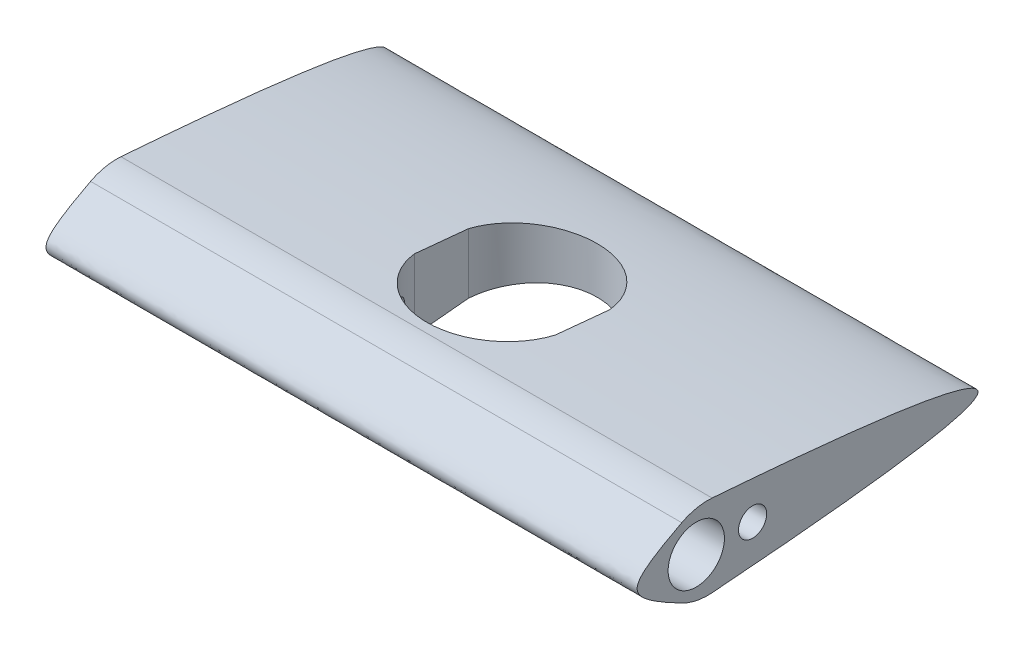
SolidWorks part; units mm, degrees
ref_plane "Front Plane" through (0, 0, 0) normal (0, 0, 1) x (1, 0, 0)
ref_plane "Top Plane" through (0, 0, 0) normal (0, 1, 0) x (1, 0, 0)
ref_plane "Right Plane" through (0, 0, 0) normal (1, 0, 0) x (0, 0, -1)
sketch "Sketch1" plane through (0, 0, 0) normal (1, 0, 0) x (0, 0, -1)
  line L0 (0, -7.6228) -> (0, 2.3772) construction
  line L1 (0, -7.5) -> (0, 7.5) construction
  line L2 (0, 0) -> (-15, 0) construction
  line L3 (0, 0) -> (50, 0) construction
  line L4 (50, 0) -> (75, 0) construction
  line L5 (75, 0) -> (100, 0) construction
  circle A0 centre (0, 0) radius 5
  circle A1 centre (10, 0) radius 2.5
  conic Q0 (0, 7.5) -> (0, -7.5) control (-15, 0) rho 0.7
  conic Q1 (0, 7.5) -> (0, -7.5) control (100, 0) rho 0.500367
  point P8 (0, 0)
  dimension "D1" = 10
  dimension "D7" = 5
  dimension "D2" = 15
  dimension "D3" = 15
  dimension "D4" = 50
  dimension "D5" = 25
  dimension "D6" = 25
  dimension "D8" = 10
extrude "Boss-Extrude1" add sketch "Sketch1" along normal blind 105
fillet "Fillet1" radius 10 2 edges at (52.5, 7.5, 0) (52.5, -7.5, 0)
sketch "Sketch2" plane through (0, 0, 0) normal (0, 1, 0) x (1, 0, 0)
  line L0 (0, 2.8086) -> (0, -2.5828) construction
  line L1 (0, -2.5828) -> (0, -10.5) construction
  line L2 (0, -10.5) -> (105, -10.5) construction
  line L3 (105, -10.5) -> (105, -2.5828) construction
  line L4 (105, -2.5828) -> (105, 2.8086) construction
  line L5 (105, 2.8086) -> (105, 50.0367) construction
  line L6 (105, 50.0367) -> (0, 50.0367) construction
  line L7 (0, 50.0367) -> (0, 2.8086) construction
  line L8 (0, 2.8086) -> (0, -2.5828)
  line L9 (0, -2.5828) -> (0, -10.5)
  line L10 (0, -10.5) -> (105, -10.5)
  line L11 (105, -10.5) -> (105, -2.5828)
  line L12 (105, -2.5828) -> (105, 2.8086)
  line L13 (105, 2.8086) -> (105, 50.0367)
  line L14 (105, 50.0367) -> (0, 50.0367)
  line L15 (0, 50.0367) -> (0, 2.8086)
  line L16 (40, 19.7683) -> (65, 19.7683) construction
  line L17 (40, -10.5) -> (65, -10.5)
  line L18 (40, -10.5) -> (40, 50.0367)
  line L19 (40, 50.0367) -> (65, 50.0367)
  line L20 (65, -10.5) -> (65, 50.0367)
  line L21 (40, -10.5) -> (65, 50.0367) construction
  line L22 (40, 50.0367) -> (65, -10.5) construction
  line L23 (52.5, 19.7683) -> (52.5, 50.0367) construction
  line L24 (52.5, -10.5) -> (52.5, 19.7683) construction
  line L25 (65, 34.9025) -> (40, 34.9025) construction
  line L26 (65, 4.6342) -> (40, 4.6342) construction
  arc A0 (40, 19.7683) -> (65, 19.7683) centre (52.5, 22.1733) cw
  arc A1 (40, 19.7683) -> (65, 19.7683) centre (52.5, 17.3634) ccw
  point P12 (52.5, 19.7683)
  point P21 (52.5, 34.9025)
  point P24 (52.5, 4.6342)
  dimension "D1" = 40
  dimension "D2" = 40
extrude "Cut-Extrude1" cut sketch "Sketch2" against normal through all both and the other way through all contours L18 A1 L20 A0
